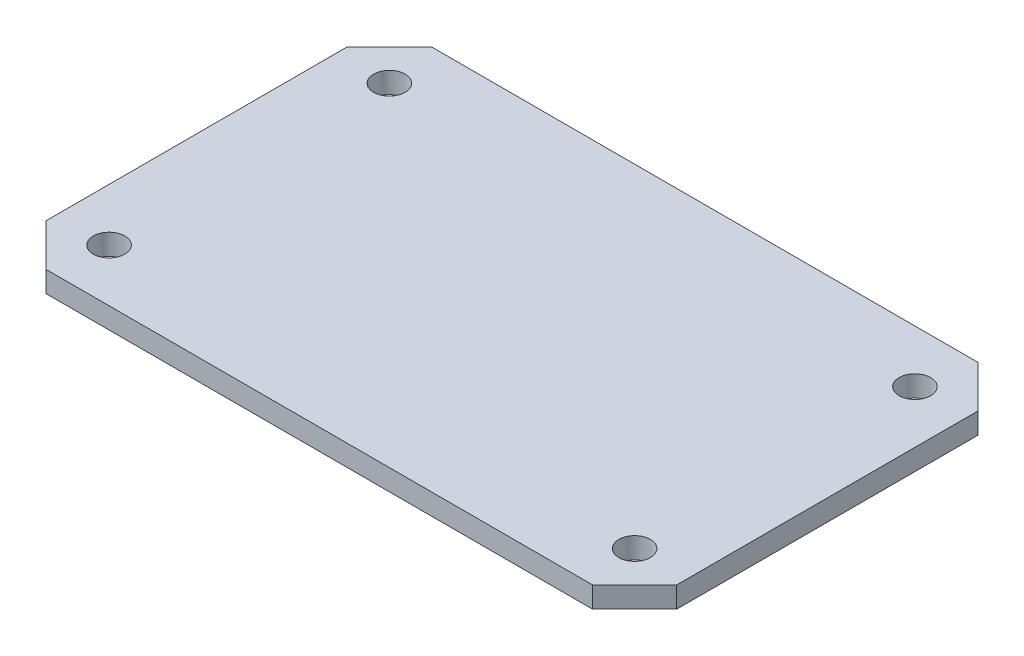
SolidWorks part; units mm, degrees
ref_plane "Front Plane" through (0, 0, 0) normal (0, 0, 1) x (1, 0, 0)
ref_plane "Top Plane" through (0, 0, 0) normal (0, 1, 0) x (1, 0, 0)
ref_plane "Right Plane" through (0, 0, 0) normal (1, 0, 0) x (0, 0, -1)
sketch "Sketch1" plane through (0, 0, 0) normal (0, 1, 0) x (1, 0, 0)
  line L1 (-45, -27.5) -> (45, -27.5)
  line L2 (-45, -27.5) -> (-45, 27.5)
  line L3 (-45, 27.5) -> (45, 27.5)
  line L4 (45, -27.5) -> (45, 27.5)
  line L5 (-45, -27.5) -> (45, 27.5) construction
  line L6 (-45, 27.5) -> (45, -27.5) construction
  point P0 (0, 0)
  dimension "D1" = 55
  dimension "D2" = 90
extrude "Boss-Extrude1" add sketch "Sketch1" along normal blind 16
sketch "Sketch2" plane through (-45, 0, 0) normal (-1, 0, 0) x (0, 0, 1)
  line L0 (-27.5, 0) -> (27.5, 0) construction
  line L1 (-17.5, 1.75) -> (17.5, 1.75)
  line L2 (-17.5, 1.75) -> (-17.5, 14.25)
  line L3 (-17.5, 14.25) -> (17.5, 14.25)
  line L4 (17.5, 1.75) -> (17.5, 14.25)
  line L5 (-17.5, 1.75) -> (17.5, 14.25) construction
  line L6 (-17.5, 14.25) -> (17.5, 1.75) construction
  line L7 (-11, -0.25) -> (11, -0.25)
  line L8 (-11, -0.25) -> (-11, 16.25)
  line L9 (-11, 16.25) -> (11, 16.25)
  line L10 (11, -0.25) -> (11, 16.25)
  line L11 (-11, -0.25) -> (11, 16.25) construction
  line L12 (-11, 16.25) -> (11, -0.25) construction
  line L13 (-27.5, 16) -> (-27.5, 0) construction
  line L14 (-11, 16.25) -> (-13, 14.25)
  line L15 (11, 16.25) -> (13, 14.25)
  line L16 (-11, -0.25) -> (-13, 1.75)
  line L17 (11, -0.25) -> (13, 1.75)
  point P0 (0, 8)
  point P5 (0, 8)
  point P14 (0, 0)
  point P17 (-27.5, 8)
  line M13 (-27.5, 0) -> (27.5, 0)
  line M15 (27.5, 16) -> (-27.5, 16)
  dimension "D1" = 22
  dimension "D2" = 12.5
  dimension "D3" = 35
  dimension "D4" = 16.5
  dimension "D5" = 45
  dimension "D6" = 45
  dimension "D7" = 45
  dimension "D8" = 45
extrude "Cut-Extrude1" cut sketch "Sketch2" against normal blind 4 contours L3 L10 L8 M15 | L15 L10 L3 M15 | L14 L3 L8 M15 | L1 L8 L3 L2 | L1 L10 L3 L8 | L10 L1 L4 L3 | L10 L1 L8 M13 | L17 L1 L10 M13 | L16 L8 L1 M13
sketch "Sketch3" plane through (-41, 0, 0) normal (-1, 0, 0) x (0, 0, 1)
  line L0 (-11, 20.75) -> (11, 20.75) construction
  line L1 (-10, 1.5) -> (10, 1.5)
  line L2 (-10, 1.5) -> (-10, 14.5)
  line L3 (-10, 14.5) -> (10, 14.5)
  line L4 (10, 1.5) -> (10, 14.5)
  line L5 (-10, 1.5) -> (10, 14.5) construction
  line L6 (-10, 14.5) -> (10, 1.5) construction
  line L7 (-17.5, 1.75) -> (-17.5, 14.25) construction
  point P0 (0, 8)
  point P7 (0, 20.75)
  point P11 (-17.5, 8)
  dimension "D1" = 20
  dimension "D2" = 13
extrude "Cut-Extrude2" cut sketch "Sketch3" against normal blind 20
chamfer "Chamfer1" distance 6 angle 45 4 edges at (45, 8, -27.5) (45, 8, 27.5) (-45, 8, 27.5) (-45, 8, -27.5)
hole_wizard "M4 Clearance Hole1" positions "Sketch5" profile "Sketch6" hole size "M4" standard "ANSI Metric" end condition through all
sketch "Sketch5" plane through (0, 16, 0) normal (0, 1, 0) x (1, 0, 0)
  line L2 (-37.5, -20) -> (37.5, -20)
  line L3 (-37.5, -20) -> (-37.5, 20)
  line L4 (-37.5, 20) -> (37.5, 20)
  line L5 (37.5, -20) -> (37.5, 20)
  line L6 (-37.5, -20) -> (37.5, 20) construction
  line L7 (-37.5, 20) -> (37.5, -20) construction
  point P3 (0, 0)
  point P4 (37.5, 20)
  point P105 (-37.5, -20)
  point P106 (-37.5, 20)
  point P107 (37.5, -20)
  dimension "D1" = 75
  dimension "D2" = 40
sketch "Sketch6" plane through (0, 16, 0) normal (1, 0, 0) x (0, 0, 1)
  line L0 (0, 0) -> (0, 16)
  line L1 (0, 16) -> (2.25, 16)
  line L2 (2.25, 16) -> (2.25, 0)
  line L5 (2.25, 0) -> (0, 0)
  line L11 (0, -6.35) -> (0, 107.95) construction
  dimension "Thru Hole Dia." = 4.5
  dimension "Thru Hole Depth" = 16
sketch "Sketch7" plane through (45, 0, 0) normal (1, 0, 0) x (0, 0, -1)
  line L0 (-21.5, 0) -> (21.5, 0) construction
  line L1 (-13.75, 3.75) -> (13.75, 3.75)
  line L2 (-13.75, 3.75) -> (-13.75, 12.25)
  line L3 (-13.75, 12.25) -> (13.75, 12.25)
  line L4 (13.75, 3.75) -> (13.75, 12.25)
  line L5 (-13.75, 3.75) -> (13.75, 12.25) construction
  line L6 (-13.75, 12.25) -> (13.75, 3.75) construction
  line L7 (-21.5, 16) -> (-21.5, 0) construction
  point P0 (0, 8)
  point P5 (0, 0)
  point P8 (0, 0)
  point P11 (-21.5, 8)
  dimension "D1" = 8.5
  dimension "D2" = 27.5
extrude "Cut-Extrude3" cut sketch "Sketch7" against normal blind 3
sketch "Sketch8" plane through (42, 0, 0) normal (1, 0, 0) x (0, 0, -1)
  line L0 (13.75, 12.25) -> (-13.75, 12.25) construction
  line L1 (-8.25, 3.75) -> (8.25, 3.75)
  line L2 (-8.25, 3.75) -> (-8.25, 12.25)
  line L3 (-8.25, 12.25) -> (8.25, 12.25)
  line L4 (8.25, 3.75) -> (8.25, 12.25)
  line L5 (-8.25, 3.75) -> (8.25, 12.25) construction
  line L6 (-8.25, 12.25) -> (8.25, 3.75) construction
  line L7 (-13.75, 3.75) -> (13.75, 3.75) construction
  point P0 (0, 8)
  point P9 (0, 0)
  point P10 (0, 3.75)
  dimension "D1" = 16.5
extrude "Cut-Extrude4" cut sketch "Sketch8" against normal blind 12
sketch "Sketch9" plane through (0, 16, 0) normal (0, 1, 0) x (1, 0, 0)
  line L24 (40, -19.4289) -> (40, 19.4289)
  line L25 (40, 19.4289) -> (36.9289, 22.5)
  line L26 (36.9289, 22.5) -> (-36.9289, 22.5)
  line L27 (-36.9289, 22.5) -> (-40, 19.4289)
  line L28 (-40, 19.4289) -> (-40, 16.25)
  line L29 (-40, 16.25) -> (-36, 16.25)
  line L30 (-36, 16.25) -> (-36, -16.25)
  line L31 (-36, -16.25) -> (-40, -16.25)
  line L32 (-40, -16.25) -> (-40, -19.4289)
  line L33 (-40, -19.4289) -> (-36.9289, -22.5)
  line L34 (-36.9289, -22.5) -> (36.9289, -22.5)
  line L35 (36.9289, -22.5) -> (40, -19.4289)
  line L36 (40, -19.4289) -> (40, 19.4289)
  line L37 (40, 19.4289) -> (36.9289, 22.5)
  line L38 (36.9289, 22.5) -> (-36.9289, 22.5)
  line L39 (-36.9289, 22.5) -> (-40, 19.4289)
  line L40 (-40, 19.4289) -> (-40, 16.25)
  line L41 (-40, 16.25) -> (-36, 16.25)
  line L42 (-36, 16.25) -> (-36, -16.25)
  line L43 (-36, -16.25) -> (-40, -16.25)
  line L44 (-40, -16.25) -> (-40, -19.4289)
  line L45 (-40, -19.4289) -> (-36.9289, -22.5)
  line L46 (-36.9289, -22.5) -> (36.9289, -22.5)
  line L47 (36.9289, -22.5) -> (40, -19.4289)
  line L79 (30, -12.5) -> (40, -12.5)
  line L80 (30, -12.5) -> (30, -22.5)
  line L81 (30, -22.5) -> (40, -22.5)
  line L82 (40, -12.5) -> (40, -22.5)
  line L83 (-30, -12.5) -> (-40, -12.5)
  line L84 (-30, -12.5) -> (-30, -22.5)
  line L85 (-30, -22.5) -> (-40, -22.5)
  line L86 (-40, -12.5) -> (-40, -22.5)
  line L87 (-30, 12.5) -> (-40, 12.5)
  line L88 (-30, 12.5) -> (-30, 22.5)
  line L89 (-30, 22.5) -> (-40, 22.5)
  line L90 (-40, 12.5) -> (-40, 22.5)
  line L91 (30, 12.5) -> (40, 12.5)
  line L92 (30, 12.5) -> (30, 22.5)
  line L93 (30, 22.5) -> (40, 22.5)
  line L94 (40, 12.5) -> (40, 22.5)
  circle M29 centre (0, 0) radius 2.25
  dimension "D2" = 10
  dimension "D1" = 5
extrude "Cut-Extrude5" cut sketch "Sketch9" against normal through all contours L91 L92 L38 L88 L87 L42 L83 L84 L46 L80 L79 L36 M29
chamfer "Chamfer2" distance 5 angle 45 4 edges at (-30, 8, -12.5) (-30, 8, 12.5) (30, 8, -12.5) (30, 8, 12.5)
sketch "Sketch10" plane through (0, 16, 0) normal (0, 1, 0) x (1, 0, 0)
  line L0 (-45, 11.25) -> (-45, -11.25)
  line L12 (45, -21.5) -> (45, 21.5)
  line L13 (45, 21.5) -> (39, 27.5)
  line L14 (39, 27.5) -> (-39, 27.5)
  line L15 (-39, 27.5) -> (-45, 21.5)
  line L16 (-45, 21.5) -> (-45, 11.25)
  line L17 (-45, 11.25) -> (-41, 11.25)
  line L18 (-41, 11.25) -> (-41, -11.25)
  line L19 (-41, -11.25) -> (-45, -11.25)
  line L20 (-45, -11.25) -> (-45, -21.5)
  line L21 (-45, -21.5) -> (-39, -27.5)
  line L22 (-39, -27.5) -> (39, -27.5)
  line L23 (39, -27.5) -> (45, -21.5)
  line L24 (45, -21.5) -> (45, 21.5)
  line L25 (45, 21.5) -> (39, 27.5)
  line L26 (39, 27.5) -> (-39, 27.5)
  line L27 (-39, 27.5) -> (-45, 21.5)
  line L28 (-45, 21.5) -> (-45, 11.25)
  line L29 (-45, 11.25) -> (-41, 11.25)
  line L30 (-41, 11.25) -> (-41, -11.25)
  line L31 (-41, -11.25) -> (-45, -11.25)
  line L32 (-45, -11.25) -> (-45, -21.5)
  line L33 (-45, -21.5) -> (-39, -27.5)
  line L34 (-39, -27.5) -> (39, -27.5)
  line L35 (39, -27.5) -> (45, -21.5)
  circle A0 centre (-37.5, -20) radius 2.25 construction
  circle A1 centre (37.5, -20) radius 2.25 construction
  circle A2 centre (37.5, 20) radius 2.25 construction
  circle A3 centre (-37.5, 20) radius 2.25 construction
  circle A4 centre (-37.5, -20) radius 2.25
  circle A5 centre (37.5, -20) radius 2.25
  circle A6 centre (37.5, 20) radius 2.25
  circle A7 centre (-37.5, 20) radius 2.25
  line M13 (45, -21.5) -> (45, 21.5)
  line M14 (45, 21.5) -> (39, 27.5)
  line M15 (39, 27.5) -> (-39, 27.5)
  line M16 (-39, 27.5) -> (-45, 21.5)
  line M17 (-45, 21.5) -> (-45, 11.25)
  line M18 (-45, 11.25) -> (-41, 11.25)
  line M19 (-41, 11.25) -> (-41, -11.25)
  line M20 (-41, -11.25) -> (-45, -11.25)
  line M21 (-45, -11.25) -> (-45, -21.5)
  line M22 (-45, -21.5) -> (-39, -27.5)
  line M23 (-39, -27.5) -> (39, -27.5)
  line M24 (39, -27.5) -> (45, -21.5)
  circle M25 centre (37.5, -20) radius 2.25
  circle M26 centre (-37.5, 20) radius 2.25
  circle M27 centre (-37.5, -20) radius 2.25
  circle M28 centre (37.5, 20) radius 2.25
  line M29 (-36, 12.5) -> (-35, 12.5)
  line M30 (-35, 12.5) -> (-30, 17.5)
  line M31 (-30, 17.5) -> (-30, 22.5)
  line M32 (-30, 22.5) -> (30, 22.5)
  line M33 (30, 22.5) -> (30, 17.5)
  line M34 (30, 17.5) -> (35, 12.5)
  line M35 (35, 12.5) -> (40, 12.5)
  line M36 (40, 12.5) -> (40, -12.5)
  line M37 (40, -12.5) -> (35, -12.5)
  line M38 (35, -12.5) -> (30, -17.5)
  line M39 (30, -17.5) -> (30, -22.5)
  line M40 (30, -22.5) -> (-30, -22.5)
  line M41 (-30, -22.5) -> (-30, -17.5)
  line M42 (-30, -17.5) -> (-35, -12.5)
  line M43 (-35, -12.5) -> (-36, -12.5)
  line M44 (-36, -12.5) -> (-36, 12.5)
  dimension "D1" = 0
extrude "Boss-Extrude2" add sketch "Sketch10" along normal blind 3 separate body contours L0 M18 M20 M19 | M24 M13 M14 M15 M16 M17 M18 M19 M20 M21 M22 M23 M25 M27 M44 M29 M30 M31 M32 M33 M34 M35 M36 M37 M38 M39 M40 M41 M42 M43 M28 M26 | M29 M44 M43 M42 M41 M40 M39 M38 M37 M36 M35 M34 M33 M32 M31 M30
delete or keep bodies "Body-Delete/Keep 1" type delete bodies bodies 108
